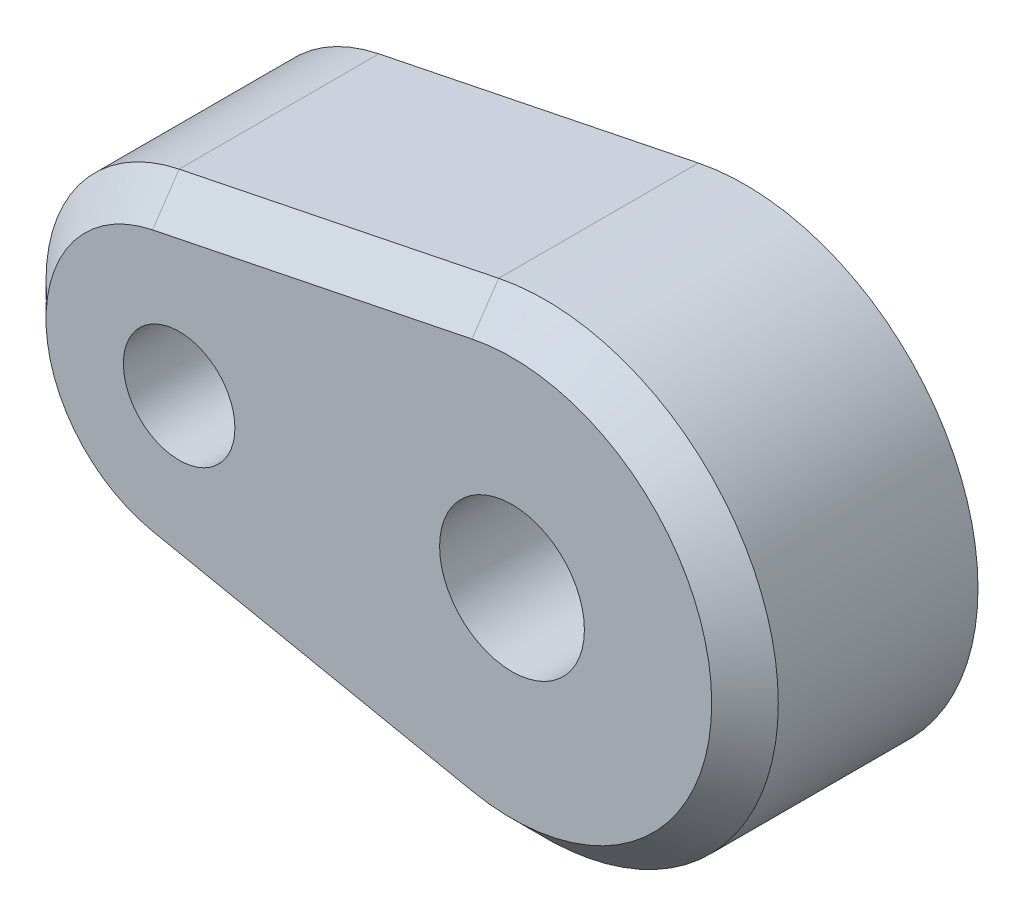
SolidWorks part; units mm, degrees
material "ABS"
ref_plane "Front Plane" through (0, 0, 0) normal (0, 0, 1) x (1, 0, 0)
ref_plane "Top Plane" through (0, 0, 0) normal (0, 1, 0) x (1, 0, 0)
ref_plane "Right Plane" through (0, 0, 0) normal (1, 0, 0) x (0, 0, -1)
sketch "Sketch1" plane through (0, 0, 0) normal (0, 0, 1) x (1, 0, 0)
  line L0 (0, 0) -> (-10, 0) construction
  line L1 (2.3094, -4) -> (4.6188, 0) construction
  line L2 (4.6188, 0) -> (2.3094, 4) construction
  line L3 (2.3094, 4) -> (-2.3094, 4) construction
  line L4 (-2.3094, 4) -> (-4.6188, 0) construction
  line L5 (-4.6188, 0) -> (-2.3094, -4) construction
  line L6 (-2.3094, -4) -> (2.3094, -4) construction
  line L7 (-1.4, 6.8586) -> (-11, 4.899)
  line L8 (-11, -4.899) -> (-1.4, -6.8586)
  circle A0 centre (0, 0) radius 2.175
  circle A1 centre (0, 0) radius 4 construction
  arc A2 (-1.4, -6.8586) -> (-1.4, 6.8586) centre (0, 0) ccw
  circle A3 centre (0, 0) radius 5 construction
  circle A4 centre (-10, 0) radius 1.675
  arc A5 (-11, 4.899) -> (-11, -4.899) centre (-10, 0) ccw
  dimension "D1" = 10
  dimension "D2" = 4.35
  dimension "D3" = 8
  dimension "D4" = 10
  dimension "D5" = 14
  dimension "D6" = 3.35
  dimension "D7" = 10
extrude "Boss-Extrude1" add sketch "Sketch1" along normal blind 7
sketch "Sketch2" plane through (0, 0, 0) normal (0, 0, -1) x (-1, 0, 0)
  circle A0 centre (0, 0) radius 4.35
  dimension "D1" = 8.7
extrude "Cut-Extrude1" cut sketch "Sketch2" against normal blind 3.4
chamfer "Chamfer1" distance 1 angle 45 4 edges at (-15, 0, 7) (-6.2, -5.8788, 7) (-6.2, 5.8788, 7) (7, 0, 7)
chamfer "Chamfer2" distance 0.5 angle 45 2 edges at (-8.325, 0, 0) (-4.35, 0, 0)
